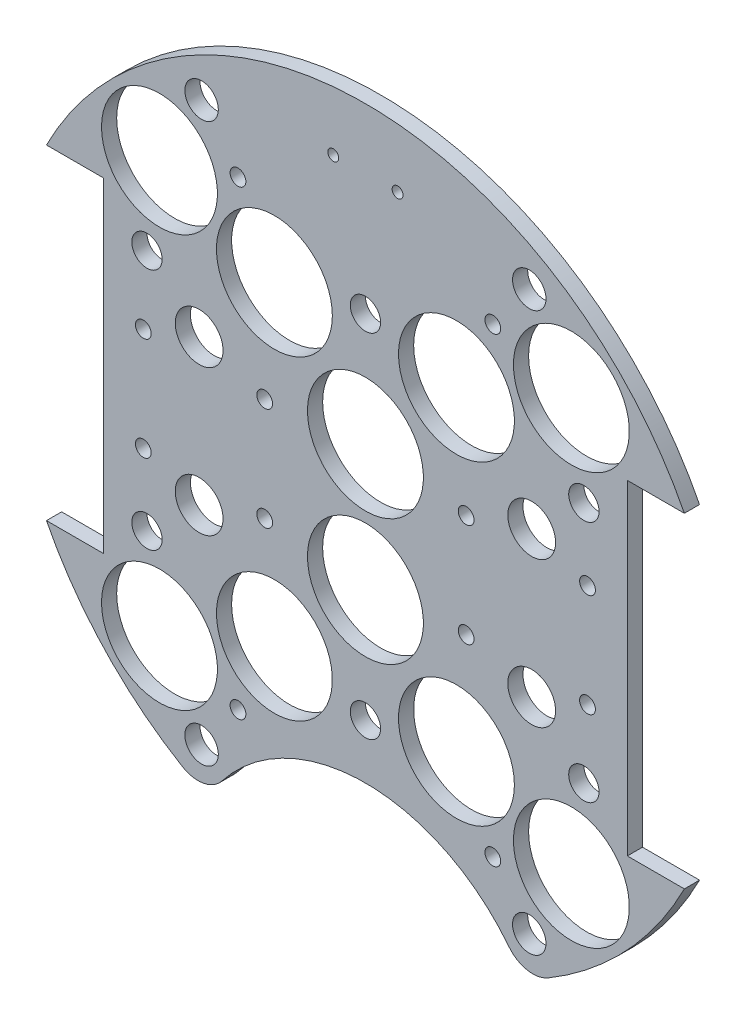
SolidWorks part; units mm, degrees
ref_plane "Front Plane" through (0, 0, 0) normal (0, 0, 1) x (1, 0, 0)
ref_plane "Top Plane" through (0, 0, 0) normal (0, 1, 0) x (1, 0, 0)
ref_plane "Right Plane" through (0, 0, 0) normal (1, 0, 0) x (0, 0, -1)
sketch "Sketch1" plane through (0, 0, 0) normal (0, 0, 1) x (1, 0, 0)
  line L0 (0, 0) -> (-82.1241, 0) construction
  line L1 (0, 0) -> (0, 95.6219) construction
  line L2 (0, -97.5637) -> (0, 139.5774) construction
  line L3 (-66.7537, 34.036) -> (-54.8157, 34.036)
  line L5 (-66.7537, -34.036) -> (-54.8157, -34.036)
  line L6 (-54.8157, 34.036) -> (-54.8157, -34.036)
  line L7 (66.7537, -34.036) -> (54.8157, -34.036)
  line L8 (66.7537, 34.036) -> (54.8157, 34.036)
  line L9 (54.8157, 34.036) -> (54.8157, -34.036)
  arc A0 (-66.7537, -34.036) -> (66.7537, -34.036) centre (0, 0) ccw
  circle A1 centre (-46.482, 10.795) radius 1.651
  circle A2 centre (-21.082, 10.795) radius 1.651
  circle A3 centre (-21.082, -10.795) radius 1.651
  circle A4 centre (-46.482, -10.795) radius 1.651
  circle A5 centre (46.482, -10.795) radius 1.651
  circle A6 centre (21.082, -10.795) radius 1.651
  circle A7 centre (21.082, 10.795) radius 1.651
  circle A8 centre (46.482, 10.795) radius 1.651
  arc A9 (66.7537, 34.036) -> (-66.7537, 34.036) centre (0, 0) ccw
  dimension "D2" = 3.302
  dimension "D3" = 3.302
  dimension "D4" = 25.4
  dimension "D5" = 10.795
  dimension "D10" = 46.482
  dimension "D12" = 10.795
  dimension "D6" = 68.072
  dimension "D7" = 11.938
  dimension "D8" = 74.93
  dimension "D9" = 74.93
  dimension "D11" = 34.036
extrude "Boss-Extrude2" add sketch "Sketch1" along normal blind 3.175
sketch "Sketch2" plane through (0, 0, 3.175) normal (0, 0, 1) x (1, 0, 0)
  line L0 (0, 68.58) -> (0, 55.88) construction
  line L1 (-9.525, 68.58) -> (9.525, 68.58)
  line L2 (-9.525, 68.58) -> (-9.525, 55.88)
  line L3 (-9.525, 55.88) -> (9.525, 55.88)
  line L4 (9.525, 68.58) -> (9.525, 55.88)
  line L5 (-9.525, 62.23) -> (9.525, 62.23) construction
  arc A0 (66.7537, 34.036) -> (-66.7537, 34.036) centre (0, 0) ccw construction
  circle A1 centre (-21.082, 10.795) radius 1.651 construction
  circle A2 centre (21.082, 10.795) radius 1.651 construction
  circle A3 centre (-6.731, 62.23) radius 1.143
  circle A4 centre (6.731, 62.23) radius 1.143
  dimension "D4" = 2.286
  dimension "D5" = 0
  dimension "D6" = 6.731
  dimension "D1" = 19.05
  dimension "D2" = 12.7
  dimension "D3" = 55.88
extrude "Cut-Extrude1" cut sketch "Sketch2" against normal through all contours A3 | A4
sketch "Sketch3" plane through (0, 0, 0) normal (0, 0, -1) x (-1, 0, 0)
  line L0 (0, 0) -> (0, -116.2908) construction
  line L1 (0, 0) -> (-153.8039, 0) construction
  line L2 (0, 0) -> (15.2681, -56.9814) construction
  line L3 (0, 0) -> (15.2302, -26.3795) construction
  circle A1 centre (0, -13.208) radius 12.1285
  circle A2 centre (0, 13.208) radius 12.1285
  circle A4 centre (-43.1052, -43.1052) radius 12.1285
  circle A6 centre (19.05, -32.9956) radius 12.1285
  circle A7 centre (19.05, 32.9956) radius 12.1285
  circle A8 centre (-43.1052, 43.1052) radius 12.1285
  circle A11 centre (43.1052, 43.1052) radius 12.1285
  circle A12 centre (-19.05, 32.9956) radius 12.1285
  circle A13 centre (-19.05, -32.9956) radius 12.1285
  circle A14 centre (43.1052, -43.1052) radius 12.1285
  point P36 (0, 0)
  point P53 (0, 0)
  point P55 (0, 0)
  dimension "D1" = 24.257
  dimension "D2" = 24.257
  dimension "D4" = 15
  dimension "D6" = 0
  dimension "D8" = 24.257
  dimension "D9" = 30
  dimension "D10" = 13.208
  dimension "D11" = 13.208
extrude "Cut-Extrude2" cut sketch "Sketch3" against normal through all
sketch "Sketch4" plane through (0, 0, 0) normal (0, 0, -1) x (-1, 0, 0)
  line L0 (33.02, -67.2621) -> (-33.02, -67.2621)
  line L1 (0, 0) -> (0, -124.2152) construction
  arc A2 (-66.7537, -34.036) -> (66.7537, -34.036) centre (0, 0) ccw construction
  circle A3 centre (0, -86.3121) radius 38.1
  point P2 (0, -67.2621)
  dimension "D4" = 76.2
  dimension "D1" = 66.04
  dimension "D2" = 74.93
  dimension "D3" = 0
  dimension "D5" = 19.05
extrude "Cut-Extrude3" cut sketch "Sketch4" against normal blind 124.46 contours A3
sketch "Sketch5" plane through (0, 0, 0) normal (0, 0, -1) x (-1, 0, 0)
  line L0 (0, 0) -> (0, -56.1647) construction
  line L1 (0, 0) -> (59.6113, 0) construction
  circle A0 centre (34.798, -15.24) radius 5
  circle A1 centre (-34.798, -15.24) radius 5
  circle A2 centre (-34.798, 15.24) radius 5
  circle A3 centre (34.798, 15.24) radius 5
  dimension "D1" = 10
  dimension "D2" = 15.24
  dimension "D3" = 34.798
extrude "Cut-Extrude4" cut sketch "Sketch5" against normal through all
extrude "Cut-Extrude5" cut sketch "Sketch6" against normal through all
sketch "Sketch6" plane through (31.3134, 132.614, 0) normal (0, 0, -1) x (0, 1, 0)
  line L0 (-132.614, -31.3134) -> (-245.9178, -31.3134) construction
  line L1 (-132.614, -31.3134) -> (-132.614, -129.4011) construction
  circle A0 centre (-180.874, -4.6434) radius 1.651
  circle A3 centre (-180.874, -57.9834) radius 1.651
  circle A4 centre (-84.354, -57.9834) radius 1.651
  circle A5 centre (-84.354, -4.6434) radius 1.651
extrude "Cut-Extrude6" cut sketch "Sketch7" against normal through all both and the other way through all
sketch "Sketch7" plane through (31.3134, 132.614, -31.75) normal (0, 0, -1) x (0, 1, 0)
  line L0 (-132.614, -31.3134) -> (-132.614, 57.8454) construction
  line L1 (-132.614, -31.3134) -> (-222.516, -31.3134) construction
  circle A0 centre (-158.014, 14.4066) radius 3.175
  circle A1 centre (-169.444, -31.3134) radius 3.175
  circle A3 centre (-158.014, -77.0334) radius 3.175
  circle A4 centre (-107.214, -77.0334) radius 3.175
  circle A5 centre (-95.784, -31.3134) radius 3.175
  circle A6 centre (-107.214, 14.4066) radius 3.175
fillet "Fillet1" radius 6.35 2 edges at (33.001, -67.2714, 1.5875) (-33.001, -67.2714, 1.5875)
extrude "Cut-Extrude7" cut sketch "Sketch8" against normal blind 29.21
sketch "Sketch8" plane through (31.3134, 132.614, -28.575) normal (0, 0, -1) x (0, 1, 0)
  line L0 (-132.614, -31.3134) -> (6.1626, -31.3134) construction
  line L2 (-132.614, -31.3134) -> (-132.614, -122.6589) construction
  circle A0 centre (-191.034, 2.9766) radius 1.651
  circle A2 centre (-154.839, -31.3134) radius 1.651
  circle A3 centre (-191.034, -65.6034) radius 1.651
  circle A4 centre (-110.389, -31.3134) radius 1.651
  circle A5 centre (-74.194, -65.6034) radius 1.651
  circle A6 centre (-74.194, 2.9766) radius 1.651
sketch "Sketch9" plane through (0, 0, 0) normal (0, 0, -1) x (-1, 0, 0)
  circle A0 centre (34.29, 58.42) radius 3.5
  circle A1 centre (-34.29, 58.42) radius 3.5
  circle A4 centre (-34.29, -58.42) radius 3.5
  circle A6 centre (34.29, -58.42) radius 3.5
  dimension "D1" = 7
  dimension "D2" = 7
  dimension "D5" = 7
  dimension "D6" = 7
extrude "Cut-Extrude8" cut sketch "Sketch9" against normal through all
